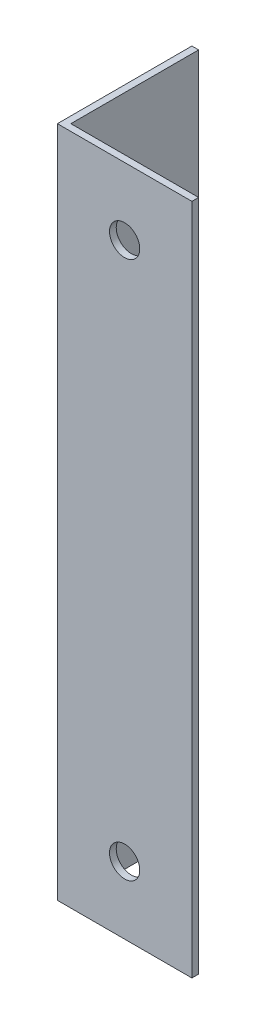
SolidWorks part; units mm, degrees
material "1060 Сплав"
ref_plane "Спереди" through (0, 0, 0) normal (0, 0, 1) x (1, 0, 0)
ref_plane "Сверху" through (0, 0, 0) normal (0, 1, 0) x (1, 0, 0)
ref_plane "Справа" through (0, 0, 0) normal (1, 0, 0) x (0, 0, -1)
sketch "Эскиз1" plane through (0, 0, 0) normal (0, 1, 0) x (1, 0, 0)
  line L0 (0, 0) -> (0, 20)
  line L1 (0, 20) -> (1, 20)
  line L2 (1, 20) -> (1, 1)
  line L3 (1, 1) -> (20, 1)
  line L4 (20, 1) -> (20, 0)
  line L5 (20, 0) -> (0, 0)
  dimension "D1" = 1
  dimension "D2" = 20
extrude "Бобышка-Вытянуть1" add sketch "Эскиз1" along normal blind 100
sketch "Эскиз2" plane through (0, 0, -1) normal (0, 0, -1) x (-1, 0, 0)
  line L0 (-20, 100) -> (-20, 0) construction
  line L1 (-20, 0) -> (-1, 0) construction
  line L2 (-20, 100) -> (-1, 100) construction
  circle A0 centre (-10, 10) radius 2.25
  circle A1 centre (-10, 90) radius 2.25
  dimension "D1" = 10
  dimension "D2" = 10
  dimension "D3" = 4.5
  dimension "D6" = 4.5
  dimension "D4" = 10
  dimension "D5" = 10
extrude "Вырез-Вытянуть1" cut sketch "Эскиз2" against normal through all
sketch "Эскиз3" plane through (1, 0, 0) normal (1, 0, 0) x (0, 0, -1)
  line L0 (10.5, 0) -> (10.5, 9.5) construction
  line L1 (1, 0) -> (20, 0) construction
  circle A0 centre (10.5, 9.5) radius 2.25
  dimension "D1" = 9.5
  dimension "D2" = 4.5
extrude "Вырез-Вытянуть2" cut sketch "Эскиз3" against normal through all
